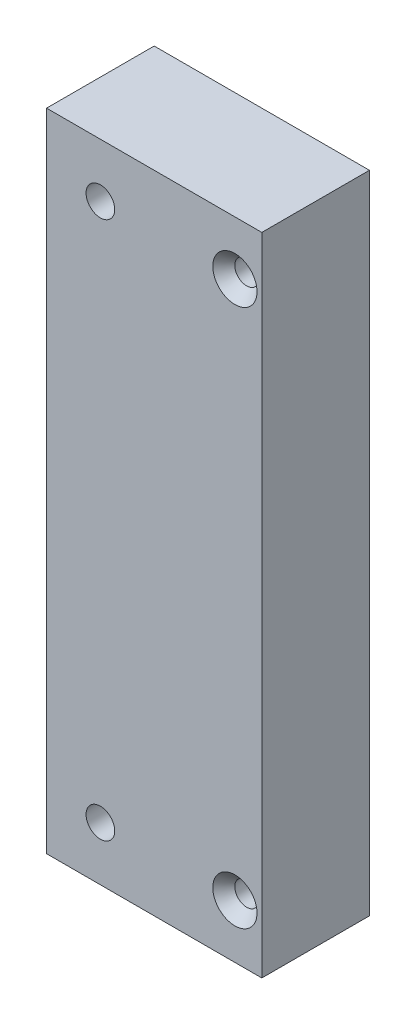
SolidWorks part; units mm, degrees
material "PE High Density"
ref_plane "Front Plane" through (0, 0, 0) normal (0, 0, 1) x (1, 0, 0)
ref_plane "Top Plane" through (0, 0, 0) normal (0, 1, 0) x (1, 0, 0)
ref_plane "Right Plane" through (0, 0, 0) normal (1, 0, 0) x (0, 0, -1)
sketch "Sketch1" plane through (0, 0, 0) normal (0, 0, 1) x (1, 0, 0)
  line L1 (0, 0) -> (1219.2, 0) construction
  line L2 (0, 0) -> (0, 1778) construction
  line L3 (0, 1778) -> (1219.2, 1778) construction
  line L4 (1219.2, 0) -> (1219.2, 1778) construction
  line L8 (355.6, 165.1) -> (355.6, 317.5)
  line L9 (355.6, 317.5) -> (304.8, 317.5)
  line L10 (304.8, 317.5) -> (304.8, 165.1)
  line L13 (355.6, 165.1) -> (304.8, 165.1)
  circle A0 centre (609.6, 241.3) radius 241.3 construction
  circle A6 centre (317.5, 304.8) radius 3.3782
  circle A7 centre (317.5, 177.8) radius 3.3782
  dimension "D3" = 609.6
  dimension "D4" = 482.6
  dimension "D10" = 6.7564
  dimension "D13" = 317.5
  dimension "D1" = 1219.2
  dimension "D2" = 1778
  dimension "D5" = 241.3
  dimension "D6" = 254
  dimension "D7" = 50.8
  dimension "D8" = 152.4
  dimension "D9" = 12.7
  dimension "D11" = 12.7
  dimension "D12" = 127
extrude "Boss-Extrude1" add sketch "Sketch1" along normal blind 25.4
sketch "Sketch2" plane through (0, 0, 25.4) normal (0, 0, 1) x (1, 0, 0)
  line L0 (355.6, 165.1) -> (355.6, 317.5) construction
  line L1 (355.6, 317.5) -> (304.8, 317.5) construction
  point P0 (349.25, 304.8)
  point P1 (349.25, 177.8)
  dimension "D1" = 6.35
  dimension "D2" = 12.7
  dimension "D3" = 127
hole_wizard "CSK for #10 Flat Head Socket Cap Screw1" positions "Sketch3" profile "Sketch4" countersink size "#10" standard "ANSI Inch" end condition through all
sketch "Sketch3" plane through (0, 0, 25.4) normal (0, 0, 1) x (1, 0, 0)
  point P0 (349.25, 304.8)
  point P3 (349.25, 177.8)
sketch "Sketch4" plane through (349.25, 304.8, 25.4) normal (1, 0, 0) x (0, -1, 0)
  line L0 (0, 0) -> (0, 25.4)
  line L1 (0, 25.4) -> (2.8067, 25.4)
  line L2 (2.8067, 25.4) -> (2.8067, 2.7758)
  line L3 (2.8067, 2.7758) -> (5.2197, 0)
  line L5 (5.2197, 0) -> (0, 0)
  line L6 (-2.8067, 2.7758) -> (-5.2197, 0) construction
  line L11 (0, -6.35) -> (0, 107.95) construction
  dimension "Thru Hole Dia." = 5.6134
  dimension "Thru Hole Depth" = 25.4
  dimension "Near C'Sink Dia." = 10.4394
  dimension "Near C'Sink Angle" = 82
